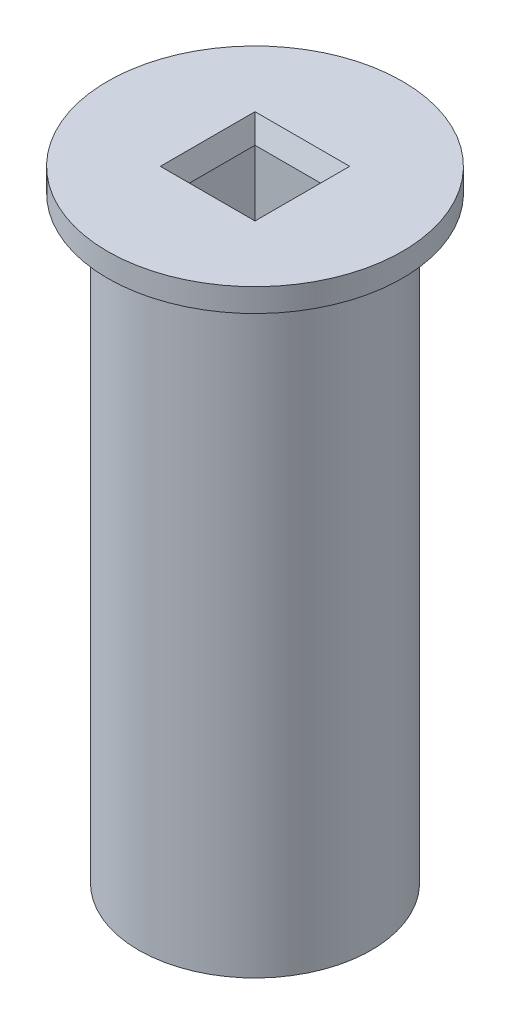
SolidWorks part; units mm, degrees
ref_plane "Спереди" through (0, 0, 0) normal (0, 0, 1) x (1, 0, 0)
ref_plane "Сверху" through (0, 0, 0) normal (0, 1, 0) x (1, 0, 0)
ref_plane "Справа" through (0, 0, 0) normal (1, 0, 0) x (0, 0, -1)
sketch "Эскиз1" plane through (0, 0, 0) normal (0, 1, 0) x (1, 0, 0)
  line L1 (5.1, -5.1) -> (-5.1, -5.1)
  line L2 (5.1, -5.1) -> (5.1, 5.1)
  line L3 (5.1, 5.1) -> (-5.1, 5.1)
  line L4 (-5.1, -5.1) -> (-5.1, 5.1)
  line L5 (5.1, -5.1) -> (-5.1, 5.1) construction
  line L6 (5.1, 5.1) -> (-5.1, -5.1) construction
  circle A0 centre (0, 0) radius 15
  dimension "D1" = 30
  dimension "D2" = 10.2
extrude "Бобышка-Вытянуть1" add sketch "Эскиз1" along normal blind 80
sketch "Sketch1" plane through (0, 80, 0) normal (0, 1, 0) x (1, 0, 0)
  line L1 (5.1, -5.1) -> (-5.1, -5.1)
  line L2 (5.1, -5.1) -> (5.1, 5.1)
  line L3 (5.1, 5.1) -> (-5.1, 5.1)
  line L4 (-5.1, -5.1) -> (-5.1, 5.1)
  line L5 (5.1, -5.1) -> (-5.1, 5.1) construction
  line L6 (5.1, 5.1) -> (-5.1, -5.1) construction
  circle A0 centre (0, 0) radius 19
  dimension "D1" = 38
extrude "Boss-Extrude1" add sketch "Sketch1" against normal blind 3
chamfer "Chamfer1" distance 1 angle 70 4 edges at (5.1, 80, 0) (0, 80, 5.1) (-5.1, 80, 0) (0, 80, -5.1)
